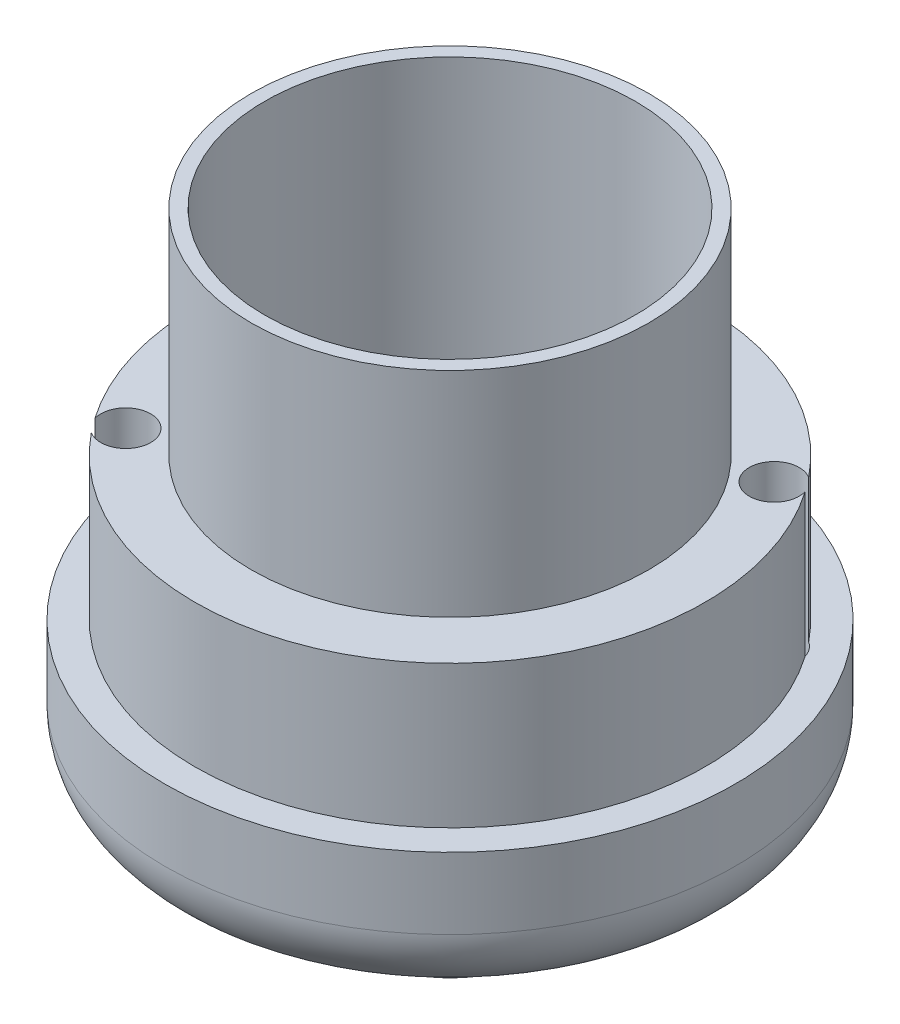
SolidWorks part; units mm, degrees
ref_plane "Front Plane" through (0, 0, 0) normal (0, 0, 1) x (1, 0, 0)
ref_plane "Top Plane" through (0, 0, 0) normal (0, 1, 0) x (1, 0, 0)
ref_plane "Right Plane" through (0, 0, 0) normal (1, 0, 0) x (0, 0, -1)
sketch "Sketch1" plane through (0, -62.1952, 0) normal (0, -1, 0) x (-1, 0, 0)
  circle A1 centre (-0.536, -73.6008) radius 17.9
  circle A2 centre (-0.536, -73.6008) radius 14.9
  dimension "D1" = 3
  dimension "D2" = 17.9
extrude "Boss-Extrude1" add sketch "Sketch1" along normal blind 10
sketch "Sketch2" plane through (0, -72.1952, 0) normal (0, -1, 0) x (-1, 0, 0)
  circle A0 centre (-0.536, -73.6008) radius 20
extrude "Boss-Extrude2" add sketch "Sketch2" along normal blind 10
fillet "Fillet1" radius 5 1 edges at (0.536, -82.1952, 53.6008)
sketch "Sketch3" plane through (0, 248.8687, 0) normal (0, 1, 0) x (1, 0, 0)
  circle A0 centre (-12.4685, -83.3448) radius 1.75
  circle A1 centre (13.5405, -63.8569) radius 1.75
extrude "Cut-Extrude1" cut sketch "Sketch3" against normal through all both and the other way through all
sketch "Sketch7" plane through (0, -82.1952, 0) normal (0, -1, 0) x (-1, 0, 0)
  line L0 (-0.536, -73.6008) -> (-13.5405, -63.8569)
  line L1 (-0.536, -73.6008) -> (12.4685, -83.3448)
  line L3 (10.5645, -85.886) -> (13.7173, -86.2644)
  line L4 (13.7173, -86.2644) -> (15.6213, -83.7231)
  line L5 (15.6213, -83.7231) -> (14.3726, -80.8035)
  line L6 (14.3726, -80.8035) -> (11.2198, -80.4252)
  line L7 (11.2198, -80.4252) -> (9.3157, -82.9664)
  line L8 (9.3157, -82.9664) -> (10.5645, -85.886)
  line L9 (-15.4446, -66.3981) -> (-12.2918, -66.7765)
  line L10 (-12.2918, -66.7765) -> (-10.3877, -64.2352)
  line L11 (-10.3877, -64.2352) -> (-11.6365, -61.3156)
  line L12 (-11.6365, -61.3156) -> (-14.7893, -60.9373)
  line L13 (-14.7893, -60.9373) -> (-16.6933, -63.4785)
  line L14 (-16.6933, -63.4785) -> (-15.4446, -66.3981)
  circle A0 centre (12.4685, -83.3448) radius 2.75 construction
  circle A1 centre (-13.5405, -63.8569) radius 2.75 construction
  dimension "D1" = 5.5
extrude "Cut-Extrude3" cut sketch "Sketch7" against normal blind 3
sketch "Sketch8" plane through (0, -62.1952, 0) normal (0, 1, 0) x (1, 0, 0)
  circle A0 centre (0.536, -73.6008) radius 13
  circle A1 centre (13.5405, -63.8569) radius 1.75
  circle A2 centre (-12.4685, -83.3448) radius 1.75
  circle A3 centre (0.536, -73.6008) radius 16.1462
  arc M5 (-11.9966, -81.6596) -> (11.7907, -63.8365) centre (0.536, -73.6008) cw
  dimension "D1" = 26
extrude "Boss-Extrude3" add sketch "Sketch8" against normal up to surface (10 mm away) contours A2 A3 A1 A0 M5 up to face at (0.536, -72.1952, 73.6008)
sketch "Sketch9" plane through (0, -82.1952, 0) normal (0, -1, 0) x (1, 0, 0)
  circle A0 centre (0.536, 73.6008) radius 6.05
  dimension "D1" = 12.1
extrude "Boss-Extrude4" add sketch "Sketch9" along normal blind 7.5
fillet "Fillet2" radius 2.5 1 edges at (0.536, -82.1952, 67.5508)
sketch "Sketch11" plane through (0, -89.6952, 0) normal (0, -1, 0) x (-1, 0, 0)
  circle A0 centre (-0.536, -73.6008) radius 2.25
  dimension "D1" = 4.5
extrude "Cut-Extrude4" cut sketch "Sketch11" against normal up to surface (17.5 mm away) up to face at (0.536, -72.1952, 60.6008)
sketch "Sketch12" plane through (0, -72.1952, 0) normal (0, 1, 0) x (1, 0, 0)
  line L1 (2.9818, -76.8182) -> (4.5452, -73.0914)
  line L2 (4.5452, -73.0914) -> (2.0995, -69.874)
  line L3 (2.0995, -69.874) -> (-1.9098, -70.3834)
  line L4 (-1.9098, -70.3834) -> (-3.4732, -74.1102)
  line L5 (-3.4732, -74.1102) -> (-1.0274, -77.3276)
  line L6 (-1.0274, -77.3276) -> (2.9818, -76.8182)
  circle A0 centre (0.536, -73.6008) radius 3.5 construction
  dimension "D1" = 7
extrude "Cut-Extrude5" cut sketch "Sketch12" against normal blind 3.5
sketch "Sketch13" plane through (0, -62.1952, 0) normal (0, 1, 0) x (1, 0, 0)
  circle A0 centre (0.536, -73.6008) radius 13
  circle A1 centre (0.536, -73.6008) radius 13.95
  dimension "D1" = 27.9
extrude "Boss-Extrude5" add sketch "Sketch13" along normal blind 15
